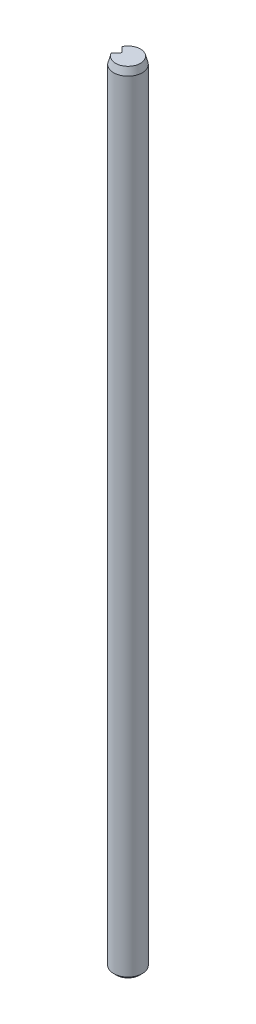
SolidWorks part; units mm, degrees
ref_plane "Front Plane" through (0, 0, 0) normal (0, 0, 1) x (1, 0, 0)
ref_plane "Top Plane" through (0, 0, 0) normal (0, 1, 0) x (1, 0, 0)
ref_plane "Right Plane" through (0, 0, 0) normal (1, 0, 0) x (0, 0, -1)
sketch "Sketch1" plane through (0, 0, 0) normal (0, 1, 0) x (1, 0, 0)
  circle A0 centre (0, 0) radius 1
  dimension "D1" = 2
extrude "Boss-Extrude1" add sketch "Sketch1" along normal blind 55
sketch "Sketch2" plane through (0, 55, 0) normal (0, 1, 0) x (1, 0, 0)
  line L0 (0, 0) -> (-1, 0) construction
  line L1 (-0.8783, 0.4781) -> (-0.4001, 0)
  line L2 (-0.4001, 0) -> (-0.8783, -0.4781)
  circle A0 centre (0, 0) radius 1 construction
  arc A1 (-0.8783, 0.4781) -> (-0.8783, -0.4781) centre (0, 0) ccw
  circle A2 centre (-1.103, 0) radius 0.497 construction
  dimension "D1" = 2.6
  dimension "D2" = 0.994
extrude "Cut-Extrude1" cut sketch "Sketch2" against normal through all
fillet "Fillet1" radius 0.1 1 edges at (-0.4001, 27.5, 0)
chamfer "Chamfer1" distance 0.5 angle 15 1 edges at (1, 55, 0)
chamfer "Chamfer2" distance 0.2 angle 45 1 edges at (1, 0, 0)
